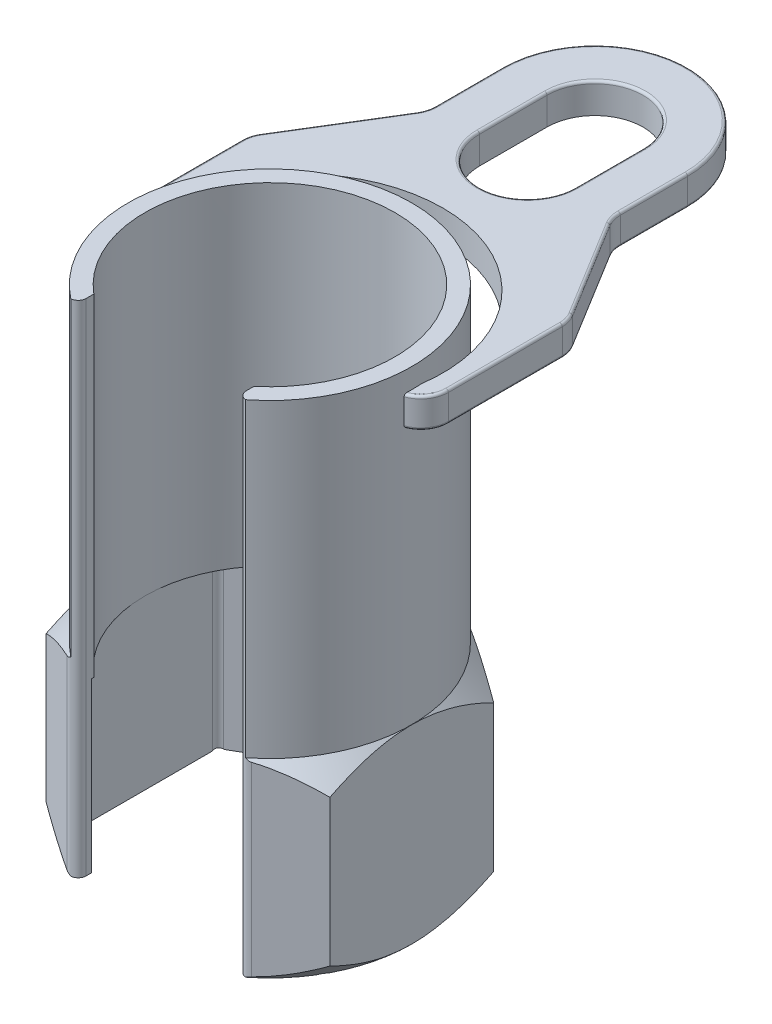
SolidWorks part; units mm, degrees
ref_plane "Front" through (0, 0, 0) normal (0, 0, 1) x (1, 0, 0)
ref_plane "Top" through (0, 0, 0) normal (0, 1, 0) x (1, 0, 0)
ref_plane "Right" through (0, 0, 0) normal (1, 0, 0) x (0, 0, -1)
sketch "Sketch1" plane through (0, 0, 0) normal (0, 1, 0) x (1, 0, 0)
  line L0 (-16, -19.2094) -> (-16, -23.5124)
  line L1 (0, 32.75) -> (-28.3623, 16.375)
  line L2 (0, 11.9615) -> (0, -7.933) construction
  line L3 (-28.3623, 16.375) -> (-28.3623, -16.375)
  line L4 (-28.3623, -16.375) -> (-16, -23.5124)
  line L5 (16, -23.5124) -> (28.3623, -16.375)
  line L6 (28.3623, -16.375) -> (28.3623, 16.375)
  line L7 (28.3623, 16.375) -> (0, 32.75)
  line L8 (16, -19.2094) -> (16, -23.5124)
  arc A0 (16, -23.4184) -> (-16, -23.4184) centre (0, 0) ccw construction
  arc A1 (16, -19.2094) -> (-16, -19.2094) centre (0, 0) ccw
  point P18 (-28.3623, -16.375)
  point P26 (28.3623, 16.375)
  dimension "D" = 65.5
  dimension "D2" = 50
  dimension "C" = 32
extrude "Extrude1" add sketch "Sketch1" along normal blind 38
sketch "Sketch3" plane through (0, 38, 0) normal (0, 1, 0) x (-1, 0, 0)
  line L0 (-28.3623, 16.375) -> (-28.3623, -16.375) construction
  line L2 (-16, 23.4183) -> (-16, 19.2094)
  line L3 (16, 23.4183) -> (16, 19.2094)
  arc A0 (-16, 19.2094) -> (16, 19.2094) centre (0, 0) ccw
  arc A1 (-16, 19.2094) -> (16, 19.2094) centre (0, 0) ccw construction
  arc A2 (-16, 23.4183) -> (16, 23.4183) centre (0, 0) ccw
  dimension "D1" = 0.0001
extrude "Extrude2" add sketch "Sketch3" along normal blind 62
sketch "Sketch8" plane through (0, 0, 0) normal (0, -1, 0) x (1, 0, 0)
  line L1 (28.3623, 16.375) -> (28.3623, -16.375) construction
  circle A0 centre (0, 0) radius 28.3623
extrude "Cut-Extrude4" cut sketch "Sketch8" against normal through all draft 45 flip side to cut
sketch "Sketch19" plane through (0, 38, 0) normal (0, 1, 0) x (-1, 0, 0)
  circle A1 centre (0, 0) radius 28.3622
  arc A2 (-16, 23.4183) -> (16, 23.4183) centre (0, 0) ccw construction
extrude "Cut-Extrude6" cut sketch "Sketch19" against normal through all draft 45 flip side to cut
sketch "Sketch26" plane through (0, 0, 0) normal (0, -1, 0) x (1, 0, 0)
  line L1 (-25, -14.4338) -> (0, -28.8675)
  line L2 (0, -28.8675) -> (25, -14.4338)
  line L3 (25, -14.4338) -> (25, 14.4338)
  line L4 (25, 14.4338) -> (0, 28.8675)
  line L5 (0, 28.8675) -> (-25, 14.4338)
  line L6 (-25, 14.4338) -> (-25, -14.4338)
  circle A0 centre (0, 0) radius 25 construction
  dimension "D1" = 50
extrude "Cut-Extrude9" cut sketch "Sketch26" against normal up to vertex (38.5 mm away)
fillet "Fillet1" radius 1.6 7 edges at (-25, 17.0587, -14.4338) (-25, 17.0587, 14.4338) (25, 17.0587, 14.4338) (25, 17.0587, -14.4338) (-16, 18.9999, 23.5124) (16, 19, 23.5124) (0, 17.0587, -28.8675)
sketch "Sketch4" [suppressed] plane through (0, 0, 0) normal (0, 1, 0) x (-1, 0, 0)
  line L0 (0, -11.2014) -> (0, 12.8888) construction
  line L1 (-10, -2.5) -> (10, -2.5)
  line L2 (-10, -2.5) -> (-10, 3.8)
  line L3 (-10, 3.8) -> (10, 3.8)
  line L4 (10, -2.5) -> (10, 3.8)
  line L5 (16.2585, 0) -> (-21.4153, 0) construction
  dimension "D1" = 50
  dimension "D2" = 9
  dimension "D3" = 7.7
sketch "Sketch12" [suppressed] plane through (0, 0, 0) normal (0, 1, 0) x (1, 0, 0)
  line L0 (-11, -4) -> (11, -4)
  line L1 (0, 0) -> (-11.4274, 0) construction
  line L2 (-11, 2.7) -> (11, 2.7)
  line L3 (-4.5, 14.3091) -> (4.5, 14.3091)
  line L4 (-7, 3.2909) -> (-7, -3.2909) construction
  line L5 (7, -3.2909) -> (7, 3.2909) construction
  arc A0 (-11, -4) -> (11, -4) centre (0, 0) ccw
  arc A1 (-6.3246, -3) -> (6.3246, -3) centre (0, 0) ccw construction
  arc A2 (-4.5, 14.3091) -> (-11, 2.7) centre (2.617, 2.7) ccw
  arc A3 (-4.5, 14.3091) -> (4.5, 14.3091) centre (0, 0) ccw construction
  arc A4 (4.5, 14.3091) -> (11, 2.7) centre (-2.617, 2.7) cw
ref_plane "Plane3" through (0, 90, 0) normal (0, 1, 0) x (-1, 0, 0)
sketch "Sketch16" plane through (0, 90, 0) normal (0, 1, 0) x (-1, 0, 0)
  line L5 (0, 0) -> (0, 54.2988) construction
  line L6 (-18.5, -65) -> (-18.5, -51.553)
  line L10 (18.5, -51.553) -> (18.5, -65)
  line L11 (31.1878, -29.3236) -> (19.3122, -48.6764)
  line L12 (-31.1878, -29.3236) -> (-19.3122, -48.6764)
  line L13 (-32, -3.6893) -> (-32, -26.447)
  line L14 (32, -3.6893) -> (32, -26.447)
  line L15 (38.3763, 1.5) -> (-38.1367, 1.5) construction
  arc A0 (-17.4785, 22.3365) -> (17.4785, 22.3365) centre (0, 0) ccw construction
  arc A1 (-28.3225, 1.5) -> (28.3225, 1.5) centre (0, 0) ccw
  arc A2 (32, -3.6893) -> (28.3225, 1.5) centre (26.5, -3.6893) ccw
  arc A3 (-32, -3.6893) -> (-28.3225, 1.5) centre (-26.5, -3.6893) cw
  arc A4 (-32, -26.447) -> (-31.1878, -29.3236) centre (-26.5, -26.447) ccw
  arc A5 (-19.3122, -48.6764) -> (-18.5, -51.553) centre (-24, -51.553) cw
  arc A7 (32, -26.447) -> (31.1878, -29.3236) centre (26.5, -26.447) cw
  arc A8 (19.3122, -48.6764) -> (18.5, -51.553) centre (24, -51.553) ccw
  arc A15 (18.5, -65) -> (-18.5, -65) centre (0, -65) cw
  point P18 (-32, -28)
  point P22 (-18.5, -50)
  point P25 (32, -28)
  point P30 (18.5, -50)
  dimension "D1" = 64
  dimension "D2" = 28
  dimension "D3" = 50
  dimension "D4" = 5.5
  dimension "D6" = 37
  dimension "D7" = 65
  dimension "D14" = 1.5
extrude "Extrude7" add sketch "Sketch16" along normal blind 6
sketch "Sketch25" plane through (0, 96, 0) normal (0, -1, 0) x (1, 0, 0)
  line L1 (-29.4486, 0) -> (37.9585, 0) construction
  line L3 (0, -57.3769) -> (0, 10.8445) construction
  line L4 (-9.6, -65) -> (-9.6, -51.5)
  line L5 (9.6, -65) -> (9.6, -51.5)
  arc A0 (-17.4785, 22.3365) -> (17.4785, 22.3365) centre (0, 0) ccw construction
  arc A2 (-18.5, -65) -> (18.5, -65) centre (0, -65) ccw construction
  arc A6 (28.2916, -2) -> (-28.2916, -2) centre (0, 0) cw
  arc A7 (28.2916, -2) -> (-28.2916, -2) centre (0, -6) cw
  arc A8 (9.6, -65) -> (-9.6, -65) centre (0, -65) cw
  arc A9 (9.6, -51.5) -> (-9.6, -51.5) centre (0, -51.5) ccw
  dimension "D1" = 32
  dimension "D2" = 19.2
  dimension "D3" = 2
  dimension "D4" = 6
extrude "Cut-Extrude8" cut sketch "Sketch25" along normal up to next
fillet "Fillet4" radius 0.5 30 edges at (9.6, 96, -58.25) (0, 96, -74.6) (-9.6, 96, -58.25) (30.9874, 96, -0.5092) (32, 96, -15.0681) (31.7931, 96, -27.9416) (-30.9874, 96, -0.5092) (-32, 96, -15.0681) (-31.7931, 96, -27.9416) (-25.25, 96, -39) (-18.7069, 96, -50.0584) (-18.5, 96, -58.2765) (0, 96, -83.5) (18.5, 96, -58.2765) (18.7069, 96, -50.0584) (30.9874, 90, -0.5092) (32, 90, -15.0681) (31.7931, 90, -27.9416) (-30.9874, 90, -0.5092) (-32, 90, -15.0681) (-31.7931, 90, -27.9416) (-25.25, 90, -39) (-18.7069, 90, -50.0584) (-18.5, 90, -58.2765) (0, 90, -83.5) (18.5, 90, -58.2765) (18.7069, 90, -50.0584) (0, 96, -41.9) (25.25, 96, -39) (25.25, 90, -39)
sketch "Sketch20" [suppressed] plane through (0, 0, 0) normal (0, 1, 0) x (1, 0, 0)
  line L0 (0, 0) -> (0, 12.8849) construction
  line L1 (-7.5, -9.3675) -> (-7.5, -14.4157)
  line L2 (7.5, -9.3675) -> (7.5, -14.4157)
  arc A0 (7.5, -14.4157) -> (-7.5, -14.4157) centre (0, 0) ccw
  arc A1 (7.5, -9.3675) -> (-7.5, -9.3675) centre (0, 0) ccw
  circle A2 centre (0, 0) radius 16.25 construction
  circle A3 centre (0, 0) radius 12 construction
  dimension "D1" = 65.5
  dimension "D2" = 50
  dimension "D3" = 32
extrude "Extrude3" [suppressed] add sketch "Sketch20" along normal blind 60
ref_plane "Plane7" [suppressed] through (0, 41.999, 0) normal (0, 1, 0) x (-1, 0, 0)
sketch "Sketch21" [suppressed] plane through (0, 41.999, 0) normal (0, 1, 0) x (-1, 0, 0)
  line L1 (2.5, 16.0565) -> (2.5, 19.8734)
  line L2 (7.5, 14.4157) -> (7.5, 9.3675) construction
  line L4 (7.5, 14.4157) -> (7.5, 18.5729)
  arc A1 (2.5, 16.0565) -> (7.5, 14.4157) centre (0, 0) ccw
  arc A2 (2.5, 19.8734) -> (7.5, 18.5729) centre (0, 0) ccw
  arc A3 (-7.5, 14.4157) -> (7.5, 14.4157) centre (0, 0) ccw construction
  dimension "D1" = 5.4
  dimension "D2" = 2.5
extrude "Extrude4" [suppressed] add sketch "Sketch21" against normal blind 17.5 separate body
ref_plane "Plane6" [suppressed] through (5.0421, 41.999, -19.385) normal (0.2517, 0, -0.9678) x (-0.9678, 0, -0.2517)
sketch "Sketch22" [suppressed] plane through (5.0421, 41.999, -19.385) normal (0.2517, 0, -0.9678) x (-0.9678, 0, -0.2517)
  line L0 (20.03, 0) -> (-20.03, 0) construction
  line L1 (0, 0) -> (0, 14.8678) construction
  line L2 (-3.2, -3.3) -> (3.2, -3.3)
  line L3 (-3.2, -3.3) -> (-3.2, -9.7)
  line L4 (-3.2, -9.7) -> (3.2, -9.7)
  line L5 (3.2, -3.3) -> (3.2, -9.7)
  line L7 (-18.9345, -6.5) -> (19.4735, -6.5) construction
  dimension "D1" = 10
  dimension "D2" = 8.75
  dimension "D3" = 10
extrude "Extrude5" [suppressed] add sketch "Sketch22" along normal blind 21 and the other way up to next
sketch "Sketch23" [suppressed] plane through (8.0628, 0, -30.9986) normal (0.2517, 0, -0.9678) x (-0.9678, 0, -0.2517)
  circle A0 centre (0, 35.499) radius 4.5255
extrude "Extrude6" [suppressed] add sketch "Sketch23" along normal blind 50 draft 2
dome "Dome1" [suppressed] faces to dome 1 distance 3 parameters "D1"=3
sketch "Sketch24" [suppressed] plane through (0, 0, 0) normal (0, -1, 0) x (1, 0, 0)
  line L2 (-12, 6.9282) -> (-12, -6.9282)
  line L3 (-12, -6.9282) -> (0, -13.8564)
  line L4 (0, -13.8564) -> (12, -6.9282)
  line L5 (12, -6.9282) -> (12, 6.9282)
  line L6 (12, 6.9282) -> (0, 13.8564)
  line L7 (0, 13.8564) -> (-12, 6.9282)
  circle A0 centre (0, 0) radius 12 construction
  dimension "D1" = 50
extrude "Cut-Extrude7" [suppressed] cut sketch "Sketch24" against normal through all
fillet "Fillet2" [suppressed] radius 0.5
fillet "Fillet3" [suppressed] radius 0.5
fillet "Fillet5" [suppressed] radius 1
